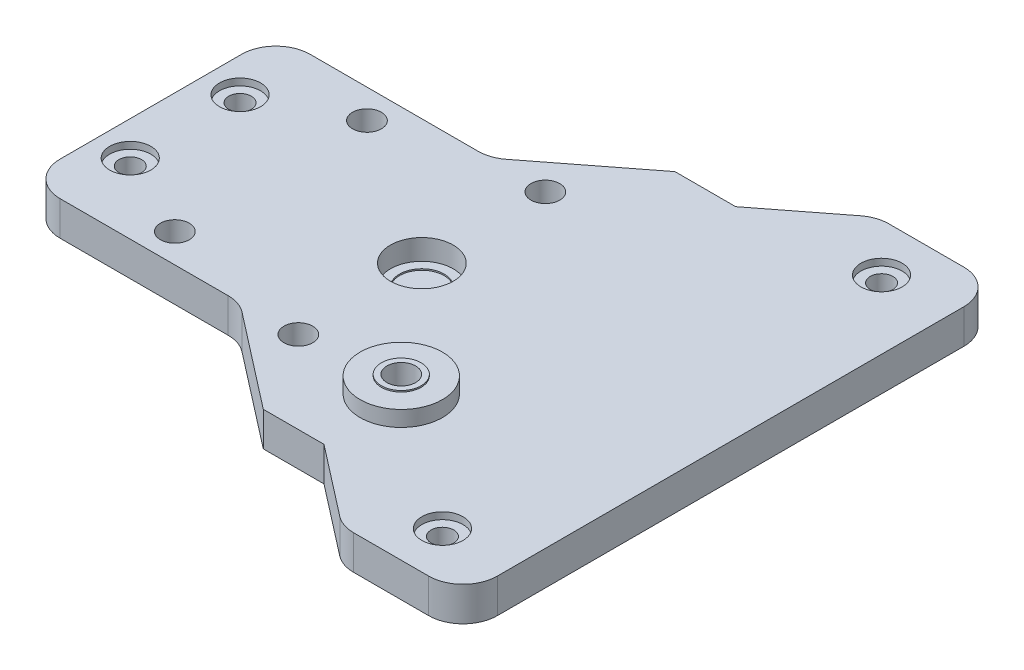
SolidWorks part; units mm, degrees
ref_plane "Front Plane" through (0, 0, 0) normal (0, 0, 1) x (1, 0, 0)
ref_plane "Top Plane" through (0, 0, 0) normal (0, 1, 0) x (1, 0, 0)
ref_plane "Right Plane" through (0, 0, 0) normal (1, 0, 0) x (0, 0, -1)
sketch "Sketch1" plane through (0, 0, 0) normal (0, 1, 0) x (1, 0, 0)
  line L0 (-22, 14) -> (-22, -14) construction
  line L1 (0, -18) -> (0, 18) construction
  line L3 (45, 30) -> (-70, 30)
  line L4 (45, 30) -> (45, -30)
  line L5 (45, -30) -> (-70, -30)
  line L6 (-70, 30) -> (-70, -30)
  circle A0 centre (-22, 14) radius 2.1
  circle A1 centre (0, 18) radius 2.1
  circle A2 centre (0, -18) radius 2.1
  circle A3 centre (-22, -14) radius 2.1
  circle A4 centre (15, -18) radius 2.1
  point P11 (-22, 0)
  point P19 (45, 0)
  dimension "D1" = 4.2
  dimension "D2" = 22
  dimension "D3" = 28
  dimension "D4" = 36
  dimension "D5" = 15
  dimension "D6" = 60
  dimension "D7" = 45
  dimension "D8" = 115
extrude "Boss-Extrude1" add sketch "Sketch1" along normal blind 5
sketch "Sketch2" plane through (0, 5, 0) normal (0, 1, 0) x (1, 0, 0)
  circle A0 centre (0, 0) radius 4.575
  dimension "D1" = 9.15
extrude "Cut-Extrude1" cut sketch "Sketch2" against normal blind 3
sketch "Sketch3" plane through (0, 2, 0) normal (0, 1, 0) x (1, 0, 0)
  circle A0 centre (0, 0) radius 3.25
  dimension "D1" = 6.5
extrude "Cut-Extrude2" cut sketch "Sketch3" against normal blind 0.2
sketch "Sketch4" plane through (0, 5, 0) normal (0, 1, 0) x (1, 0, 0)
  line L0 (-22, 18.2216) -> (-8.2975, 18.2216) construction
  line L1 (-22, -18.2216) -> (-8.2975, -18.2216) construction
  line L2 (-22, 18.2216) -> (-8.2975, 18.2216) construction
  line L3 (-22, -18.2216) -> (-8.2975, -18.2216) construction
  line L4 (-28.4216, 7.4) -> (-28.4216, 11.8) construction
  line L5 (-28.4216, -7.4) -> (-28.4216, 7.4) construction
  line L6 (-28.4216, -11.8) -> (-28.4216, -7.4) construction
  line L7 (-28.4216, 7.4) -> (-28.4216, 11.8) construction
  line L8 (-28.4216, -7.4) -> (-28.4216, 7.4) construction
  line L9 (-28.4216, -11.8) -> (-28.4216, -7.4) construction
  line L10 (-6.8288, 12.5) -> (26.8012, 38.5804) construction
  line L11 (-37.5, 12.5) -> (-6.8288, 12.5) construction
  line L14 (26.8012, -38.5804) -> (-6.8288, -12.5) construction
  line L15 (-6.8288, 12.5) -> (26.8012, 38.5804) construction
  line L16 (-37.5, 12.5) -> (-6.8288, 12.5) construction
  line L17 (-37.5, -12.5) -> (-37.5, 12.5) construction
  line L18 (-6.8288, -12.5) -> (-37.5, -12.5) construction
  line L19 (26.8012, -38.5804) -> (-6.8288, -12.5) construction
  line L20 (-34.5, 8) -> (-34.5, -8) construction
  arc A0 (-22, 18.2216) -> (-28.4216, 11.8) centre (-22, 11.8) ccw construction
  arc A1 (-28.4216, -11.8) -> (-22, -18.2216) centre (-22, -11.8) ccw construction
  arc A2 (-22, 18.2216) -> (-28.4216, 11.8) centre (-22, 11.8) ccw construction
  arc A3 (-28.4216, -11.8) -> (-22, -18.2216) centre (-22, -11.8) ccw construction
  arc A4 (-3.0173, -20.626) -> (-8.2975, -18.2216) centre (-8.2975, -25.2216) ccw construction
  arc A5 (-8.2975, 18.2216) -> (-3.0173, 20.626) centre (-8.2975, 25.2216) ccw construction
  arc A6 (-8.2975, 18.2216) -> (-3.0173, 20.626) centre (-8.2975, 25.2216) ccw construction
  arc A7 (-3.0173, -20.626) -> (-8.2975, -18.2216) centre (-8.2975, -25.2216) ccw construction
  circle A8 centre (-34.5, 8) radius 3 construction
  circle A9 centre (-34.5, -8) radius 3 construction
  circle A10 centre (-34.5, -8) radius 1.65
  circle A11 centre (-34.5, 8) radius 1.65
  point P26 (-34.5, 0)
  dimension "D1" = 6
  dimension "D2" = 3.3
  dimension "D3" = 16
  dimension "D4" = 34.5
extrude "Cut-Extrude3" cut sketch "Sketch4" against normal through all
sketch "Sketch6" plane through (0, 5, 0) normal (0, 1, 0) x (1, 0, 0)
  line L0 (-22, 18.2216) -> (-34.5, 18.2216)
  line L1 (-39.5, 13.2216) -> (-39.5, -13.2216)
  line L2 (-34.5, -18.2216) -> (-22, -18.2216)
  line L4 (-70, -30) -> (45, -30) construction
  line L5 (-22, -30) -> (-70, -30)
  line L6 (-70, -30) -> (-70, 30)
  line L7 (-70, 30) -> (-70, -30) construction
  line L8 (45, 30) -> (-70, 30) construction
  line L9 (-70, 30) -> (-22, 30)
  line L11 (-34.5, 8) -> (-34.5, -8) construction
  line L12 (-22, -18.2216) -> (-8.2975, -18.2216) construction
  line L13 (-22, 18.2216) -> (-8.2975, 18.2216) construction
  line L14 (-22, 18.2216) -> (-8.2975, 18.2216)
  line L15 (-22, -18.2216) -> (-8.2975, -18.2216)
  line L17 (26.8012, -38.5804) -> (-6.8288, -12.5) construction
  line L18 (-8.2975, -18.2216) -> (14.6355, -36.0064)
  line L21 (-8.2975, 18.2216) -> (16.0948, 37.138)
  line L22 (16.0948, 37.138) -> (-22, 30)
  line L23 (14.6355, -36.0064) -> (-22, -30)
  line L24 (-6.8288, 12.5) -> (26.8012, 38.5804) construction
  arc A0 (-34.5, 18.2216) -> (-39.5, 13.2216) centre (-34.5, 13.2216) ccw
  arc A1 (-39.5, -13.2216) -> (-34.5, -18.2216) centre (-34.5, -13.2216) ccw
  point P2 (0, 0)
  point P10 (19.0107, -37.9617)
  point P23 (-4.1468, -18)
  point P30 (-8.861, -18.2216)
  point P31 (16.0948, 37.138)
  point P33 (-8.2975, 18.851)
  point P36 (0, 0)
  dimension "D2" = 5
  dimension "D1" = 5
extrude "Cut-Extrude4" cut sketch "Sketch6" against normal through all
sketch "Sketch7" plane through (0, 5, 0) normal (0, 1, 0) x (1, 0, 0)
  line L0 (27.3422, 39) -> (15.7369, 30)
  line L1 (15.7369, 30) -> (45, 30)
  line L2 (45, 30) -> (45, 39)
  line L3 (45, -30) -> (15.7369, -30)
  line L4 (15.7369, -30) -> (27.3422, -39)
  line L5 (27.3422, -39) -> (45, -39)
  line L6 (45, -39) -> (45, -30)
  line L7 (45, 39) -> (27.3422, 39)
  line L10 (-6.8288, 12.5) -> (26.8012, 38.5804) construction
  line L11 (45, 30) -> (6.8904, 30) construction
  line L12 (26.8012, -38.5804) -> (-6.8288, -12.5) construction
  line L13 (6.8904, -30) -> (45, -30) construction
  point P2 (26.8012, 38.5804)
  point P4 (15.7369, 30)
  point P18 (15.7369, -30)
  point P24 (26.8012, -39.4196)
  point P25 (26.8012, -38.5804)
  point P27 (26.8012, -41.2176)
  point P28 (30.7714, 39.7977)
  point P29 (30.2633, -46.0814)
  dimension "D1" = 78
extrude "Boss-Extrude2" add sketch "Sketch7" against normal up to surface (5 mm away) up to face at (-6.2885, 0, 0)
sketch "Sketch8" plane through (0, 5, 0) normal (0, 1, 0) x (1, 0, 0)
  line L0 (35, 32) -> (35, -32) construction
  circle A0 centre (35, 32) radius 1.65
  circle A1 centre (35, -32) radius 1.65
  circle A2 centre (35, 32) radius 3 construction
  circle A3 centre (35, -32) radius 3 construction
  point P6 (35, 0)
  dimension "D1" = 6
  dimension "D2" = 3.3
  dimension "D3" = 35
  dimension "D4" = 64
extrude "Cut-Extrude5" cut sketch "Sketch8" against normal through all
fillet "Fillet1" radius 5 6 edges at (45, 2.5, 39) (27.3422, 2.5, 39) (27.3422, 2.5, -39) (45, 2.5, -39) (-8.2975, 2.5, 18.2216) (-8.2975, 2.5, -18.2216)
sketch "Sketch9" plane through (0, 5, 0) normal (0, 1, 0) x (1, 0, 0)
  circle A0 centre (15, -18) radius 6
  circle A1 centre (15, -18) radius 2.1 construction
  circle A2 centre (15, -18) radius 2.1
  dimension "D1" = 12
extrude "Boss-Extrude3" add sketch "Sketch9" along normal blind 2.275
sketch "Sketch10" plane through (0, 7.275, 0) normal (0, 1, 0) x (1, 0, 0)
  circle A0 centre (15, -18) radius 2.9
  circle A1 centre (15, -18) radius 2.1 construction
  circle A2 centre (15, -18) radius 2.1
  dimension "D1" = 0.8
extrude "Boss-Extrude4" add sketch "Sketch10" along normal blind 0.2
sketch "Sketch11" plane through (0, 5, 0) normal (0, 1, 0) x (1, 0, 0)
  circle A0 centre (-34.5, 8) radius 3
  circle A1 centre (-34.5, -8) radius 3
  circle A2 centre (35, -32) radius 3
  circle A3 centre (35, 32) radius 3
  dimension "D1" = 6
extrude "Cut-Extrude6" cut sketch "Sketch11" against normal blind 1
